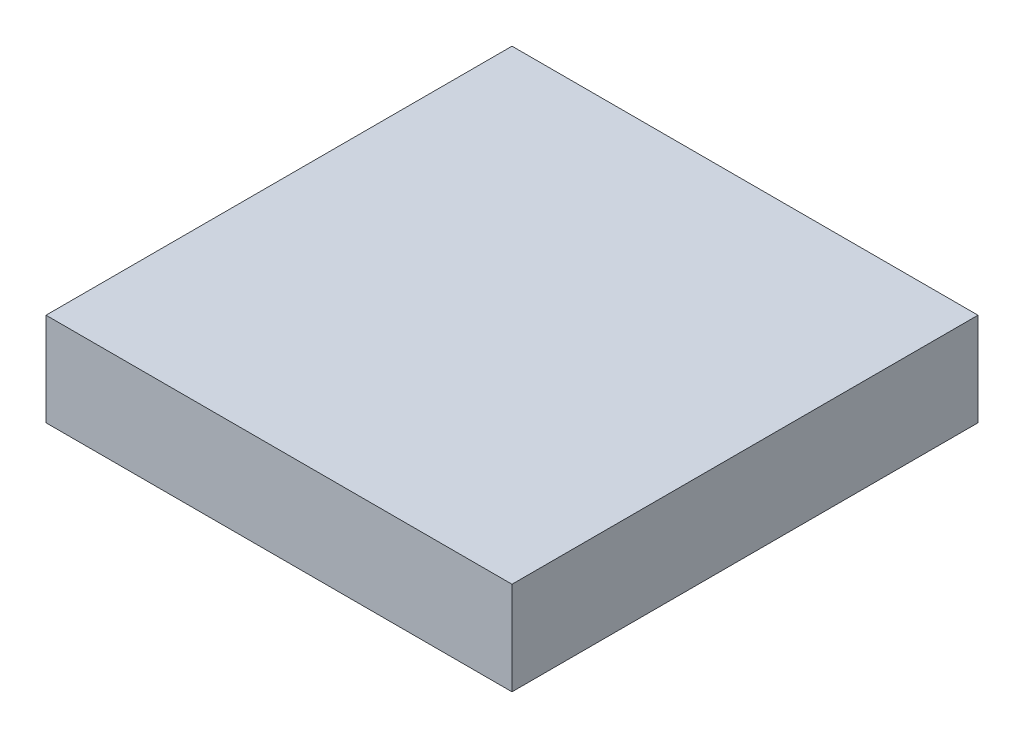
SolidWorks part; units mm, degrees
material "Custom Plastic"
ref_plane "Front Plane" through (0, 0, 0) normal (0, 0, 1) x (1, 0, 0)
ref_plane "Top Plane" through (0, 0, 0) normal (0, 1, 0) x (1, 0, 0)
ref_plane "Right Plane" through (0, 0, 0) normal (1, 0, 0) x (0, 0, -1)
sketch "Sketch1" plane through (0, 0, 0) normal (0, 1, 0) x (1, 0, 0)
  line L1 (-12.7, -12.7) -> (12.7, -12.7)
  line L2 (-12.7, -12.7) -> (-12.7, 12.7)
  line L3 (-12.7, 12.7) -> (12.7, 12.7)
  line L4 (12.7, -12.7) -> (12.7, 12.7)
  line L5 (-12.7, -12.7) -> (12.7, 12.7) construction
  line L6 (-12.7, 12.7) -> (12.7, -12.7) construction
  point P0 (0, 0)
  dimension "D1" = 25.4
extrude "Boss-Extrude1" add sketch "Sketch1" along normal blind 5.08
